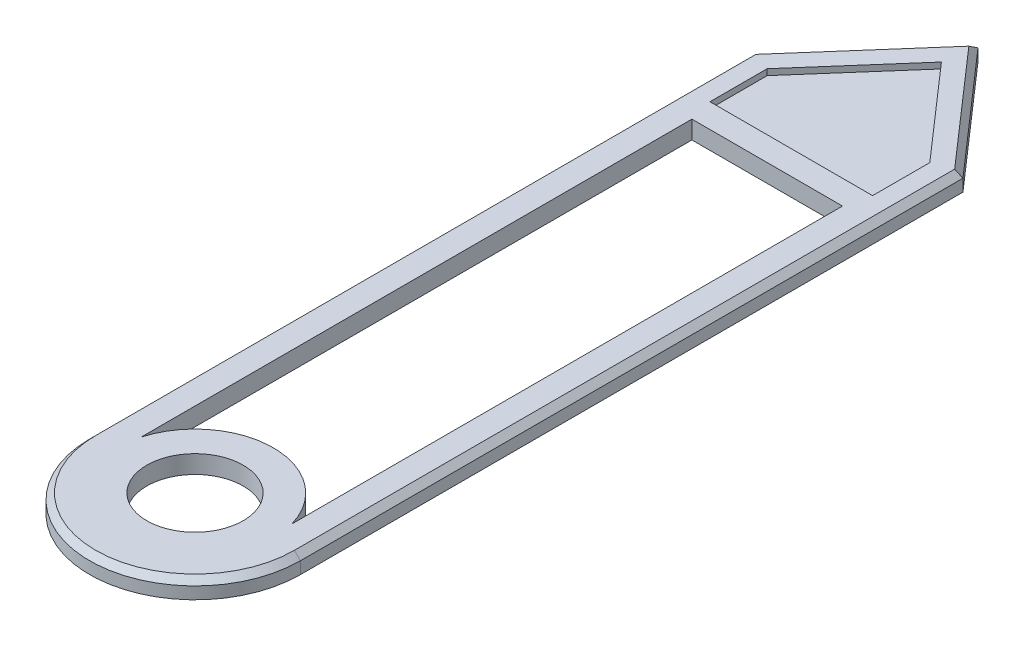
SolidWorks part; units mm, degrees
ref_plane "Front Plane" through (0, 0, 0) normal (0, 0, 1) x (1, 0, 0)
ref_plane "Top Plane" through (0, 0, 0) normal (0, 1, 0) x (1, 0, 0)
ref_plane "Right Plane" through (0, 0, 0) normal (1, 0, 0) x (0, 0, -1)
sketch "Sketch1" plane through (0, 0, 0) normal (0, 1, 0) x (1, 0, 0)
  line L0 (-1.75, 0) -> (1.75, 0) construction
  line L1 (-1.75, 0) -> (-1.75, 11)
  line L2 (0, 0) -> (0, 13) construction
  line L3 (1.75, 0) -> (1.75, 11)
  line L4 (-1.75, 11) -> (0, 13)
  line L5 (0, 13) -> (1.75, 11)
  line L6 (-1.25, 0.3571) -> (-1.25, 9.5)
  line L7 (-1.25, 9.5) -> (1.25, 9.5)
  line L8 (1.25, 9.5) -> (1.25, 0.3571)
  circle A0 centre (0, 0) radius 0.8
  arc A1 (-1.75, 0) -> (1.75, 0) centre (0, 0) ccw
  arc A2 (-1.25, 0.3571) -> (1.25, 0.3571) centre (0, 0) cw
  dimension "D1" = 1.6
  dimension "D4" = 0.5
  dimension "D2" = 3.5
  dimension "D3" = 11
  dimension "D5" = 3.5
  dimension "D6" = 0.5
  dimension "D7" = 13
extrude "Boss-Extrude1" add sketch "Sketch1" along normal blind 0.3
sketch "Sketch2" plane through (0, 0.3, 0) normal (0, 1, 0) x (1, 0, 0)
  line L7 (-1.35, 10.8497) -> (-1.35, 9.9)
  line L8 (-1.35, 9.9) -> (1.35, 9.9)
  line L9 (1.449, 10.7366) -> (0, 12.3926)
  line L10 (0, 12.3926) -> (-1.449, 10.7366)
  line L11 (1.35, 10.8497) -> (0, 12.3926)
  line L12 (0, 12.3926) -> (-1.35, 10.8497)
  line L13 (1.35, 9.9) -> (1.35, 10.8497)
  line L14 (0, 12.3926) -> (0, 9.9) construction
  line L15 (-1.75, 11) -> (-1.75, 0) construction
  line L16 (1.25, 9.5) -> (-1.25, 9.5) construction
  dimension "D2" = 0.4
  dimension "D3" = 0.4
  dimension "D1" = 0.4
extrude "Cut-Extrude1" cut sketch "Sketch2" against normal blind 0.1
chamfer "Chamfer1" distance 0.1 angle 45 5 edges at (-1.75, 0.3, -5.5) (0, 0.3, 1.75) (-0.875, 0.3, -12) (0.875, 0.3, -12) (1.75, 0.3, -5.5)
